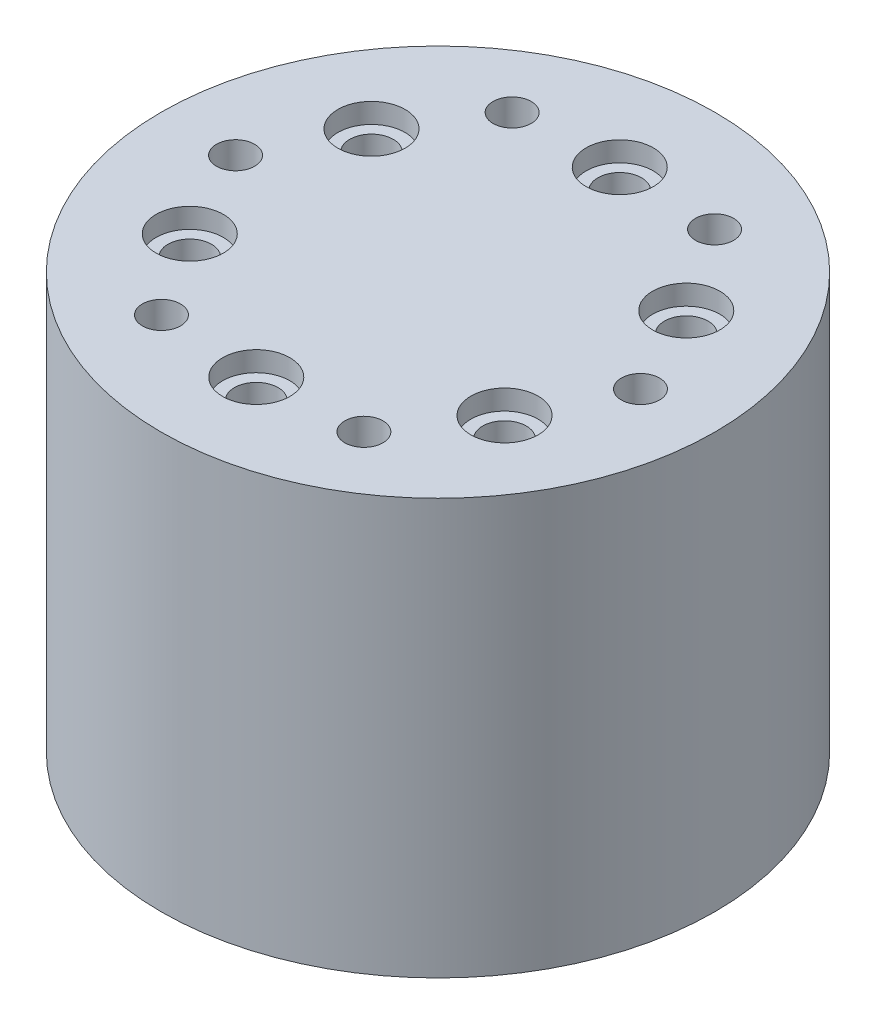
SolidWorks part; units mm, degrees
ref_plane "Front Plane" through (0, 0, 0) normal (0, 0, 1) x (1, 0, 0)
ref_plane "Top Plane" through (0, 0, 0) normal (0, 1, 0) x (1, 0, 0)
ref_plane "Right Plane" through (0, 0, 0) normal (1, 0, 0) x (0, 0, -1)
sketch "Sketch1" plane through (0, 0, 0) normal (0, 1, 0) x (1, 0, 0)
  circle A0 centre (0, 0) radius 76.2
  dimension "D1" = 152.4
extrude "Boss-Extrude1" add sketch "Sketch1" along normal blind 114.3
hole_wizard "CBORE for M10 SBHCS1" positions "Sketch3" profile "Sketch5" counterbore size "M10" standard "ANSI Metric" end condition through all
sketch "Sketch3" plane through (0, 114.3, 0) normal (0, 1, 0) x (1, 0, 0)
  line L0 (0, 0) -> (0, 50) construction
  point P0 (0, 50)
  point P11 (43.3013, 25)
  point P12 (43.3013, -25)
  point P13 (0, -50)
  point P14 (-43.3013, -25)
  point P15 (-43.3013, 25)
  dimension "D1" = 50
  dimension "D2" = 6
sketch "Sketch5" plane through (0, 114.3, -50) normal (1, 0, 0) x (0, 0, 1)
  line L0 (0, 0) -> (0, 114.3)
  line L1 (0, 114.3) -> (6, 114.3)
  line L3 (6, 114.3) -> (6, 5.5)
  line L4 (6, 5.5) -> (9.25, 5.5)
  line L5 (9.25, 5.5) -> (9.25, 0)
  line L7 (9.25, 0) -> (0, 0)
  line L11 (0, -6.35) -> (0, 107.95) construction
  dimension "Thru Hole Dia." = 12
  dimension "Thru Hole Depth" = 114.3
  dimension "C'Bore Dia." = 18.5
  dimension "C'Bore Depth" = 5.5
sketch "Sketch34" plane through (0, 114.3, 0) normal (0, 1, 0) x (1, 0, 0)
  line L0 (11.7333, -45.1399) -> (23.1119, -72.6105)
  line L1 (-11.7333, -45.1399) -> (-23.1119, -72.6105)
  line L2 (0, -50) -> (0, -76.2) construction
  circle A0 centre (0, -50) radius 12.7
  circle A3 centre (0, 0) radius 76.2 construction
  dimension "D2" = 45
  dimension "D1" = 25.4
sketch "Sketch45" plane through (0, 114.3, 0) normal (0, 1, 0) x (1, 0, 0)
  line L2 (0, 0) -> (76.2, 0) construction
  circle A1 centre (55.7, 0) radius 5.5
  circle A2 centre (0, 0) radius 76.2 construction
  dimension "D1" = 11
  dimension "D2" = 55.7
hole_wizard "Tap Drill for M10 Helicoil1" positions "Sketch46" profile "Sketch47" hole size "M10x1.5" standard "ANSI Metric"
sketch "Sketch46" plane through (0, 114.3, 0) normal (0, 1, 0) x (1, 0, 0)
  point P0 (55.7, 0)
sketch "Sketch47" plane through (55.7, 114.3, 0) normal (1, 0, 0) x (0, 0, 1)
  line L0 (0, 0) -> (0, 28.1545)
  line L1 (0, 28.1545) -> (5.25, 25)
  line L2 (5.25, 25) -> (5.25, 0)
  line L5 (5.25, 0) -> (0, 0)
  line L10 (0, 28.1545) -> (-5.25, 25) construction
  line L11 (0, -6.35) -> (0, 107.95) construction
  dimension "Hole Dia." = 10.5
  dimension "Hole Depth" = 25
  dimension "Drill Angle" = 118
pattern_circular "CirPattern1" count 6 over 360 about axis through (0, 0, 0) along (0, 1, 0) of "Tap Drill for M10 Helicoil1"
sketch "Sketch35" plane through (0, 114.3, 0) normal (0, 1, 0) x (1, 0, 0)
  circle A0 centre (0, 0) radius 37.3
  circle A1 centre (0, 0) radius 95.25
  dimension "D1" = 74.6
  dimension "D2" = 190.5
extrude "Cut-Extrude4" [suppressed] cut sketch "Sketch35" against normal up to surface (50.8 mm away)
sketch "Sketch36" plane through (0, 114.3, 0) normal (0, 1, 0) x (1, 0, 0)
  point P0 (0, 0)
